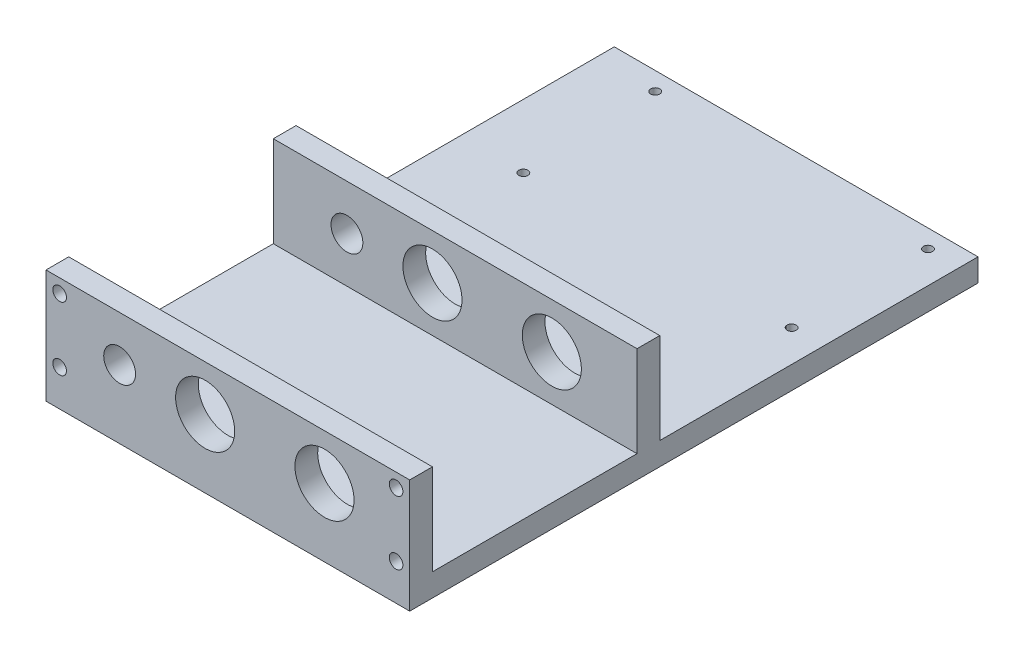
SolidWorks part; units mm, degrees
ref_plane "정면" through (0, 0, 0) normal (0, 0, 1) x (1, 0, 0)
ref_plane "윗면" through (0, 0, 0) normal (0, 1, 0) x (1, 0, 0)
ref_plane "우측면" through (0, 0, 0) normal (1, 0, 0) x (0, 0, -1)
sketch "스케치1" plane through (0, 0, 0) normal (0, 0, 1) x (1, 0, 0)
  line L0 (0, 0) -> (80, 0)
  line L3 (0, 0) -> (0, 25)
  line L4 (0, 25) -> (80, 25)
  line L5 (80, 0) -> (80, 25)
  dimension "D1" = 80
  dimension "D2" = 25
extrude "보스-돌출1" add sketch "스케치1" along normal blind 5
sketch "스케치2" plane through (0, 0, 0) normal (0, 0, -1) x (-1, 0, 0)
  line L0 (-80, 0) -> (-80, 25) construction
  line L1 (-80, 5) -> (0, 5)
  line L2 (-80, 5) -> (-80, 0)
  line L3 (-80, 0) -> (0, 0)
  line L4 (0, 5) -> (0, 0)
  dimension "D1" = 5
extrude "보스-돌출2" add sketch "스케치2" along normal blind 120
sketch "스케치3" plane through (0, 5, 0) normal (0, 1, 0) x (1, 0, 0)
  line L0 (80, 50) -> (0, 50)
  line L1 (80, 120) -> (80, 0) construction
  line L2 (0, 120) -> (0, 0) construction
  line L3 (0, 50) -> (0, 45)
  line L4 (0, 45) -> (80, 45)
  line L5 (80, 45) -> (80, 50)
  line L6 (80, -5) -> (0, -5) construction
  dimension "D1" = 55
  dimension "D2" = 5
extrude "보스-돌출3" add sketch "스케치3" along normal blind 20
sketch "스케치4" plane through (0, 0, 0) normal (0, 0, -1) x (-1, 0, 0)
  line L0 (-80, 5) -> (-80, 25) construction
  line L2 (-80, 15) -> (0, 15) construction
  line L3 (0, 25) -> (0, 5) construction
  line L4 (-40, 5) -> (-40, 25) construction
  line L5 (0, 5) -> (-80, 5) construction
  line L6 (-80, 25) -> (0, 25) construction
  circle A0 centre (-77, 22) radius 1.5
  circle A1 centre (-77, 8) radius 1.5
  circle A2 centre (-3, 22) radius 1.5
  circle A3 centre (-3, 8) radius 1.5
  dimension "D1" = 3
  dimension "D2" = 3
  dimension "D3" = 3
extrude "컷-돌출1" cut sketch "스케치4" against normal blind 20
sketch "스케치5" plane through (0, 0, 0) normal (0, 0, -1) x (-1, 0, 0)
  line L0 (-80, 15) -> (0, 15) construction
  circle A0 centre (-61.2583, 15) radius 6.5
  circle A1 centre (-35.0047, 15) radius 6.5
  dimension "D1" = 13
  dimension "D2" = 13
extrude "컷-돌출2" cut sketch "스케치5" against normal through all both and the other way through all
sketch "스케치6" plane through (0, 0, 0) normal (0, 0, -1) x (-1, 0, 0)
  line L0 (-80, 15) -> (0, 15) construction
  circle A0 centre (-16.1918, 15) radius 3.5
  dimension "D1" = 7
extrude "컷-돌출3" cut sketch "스케치6" against normal through all both and the other way through all
sketch "스케치7" plane through (0, 5, 0) normal (0, 1, 0) x (1, 0, 0)
  line L0 (80, 120) -> (80, 50) construction
  line L1 (0, 120) -> (80, 120) construction
  circle A0 centre (73, 116) radius 1
  circle A1 centre (73, 86) radius 1
  circle A4 centre (13, 116) radius 1
  circle A5 centre (14, 86) radius 1
  dimension "D1" = 2
  dimension "D4" = 2
  dimension "D6" = 7
  dimension "D7" = 2
  dimension "D10" = 2
  dimension "D2" = 7
  dimension "D3" = 4
  dimension "D5" = 30
  dimension "D8" = 60
  dimension "D9" = 4
extrude "컷-돌출4" cut sketch "스케치7" against normal blind 20
